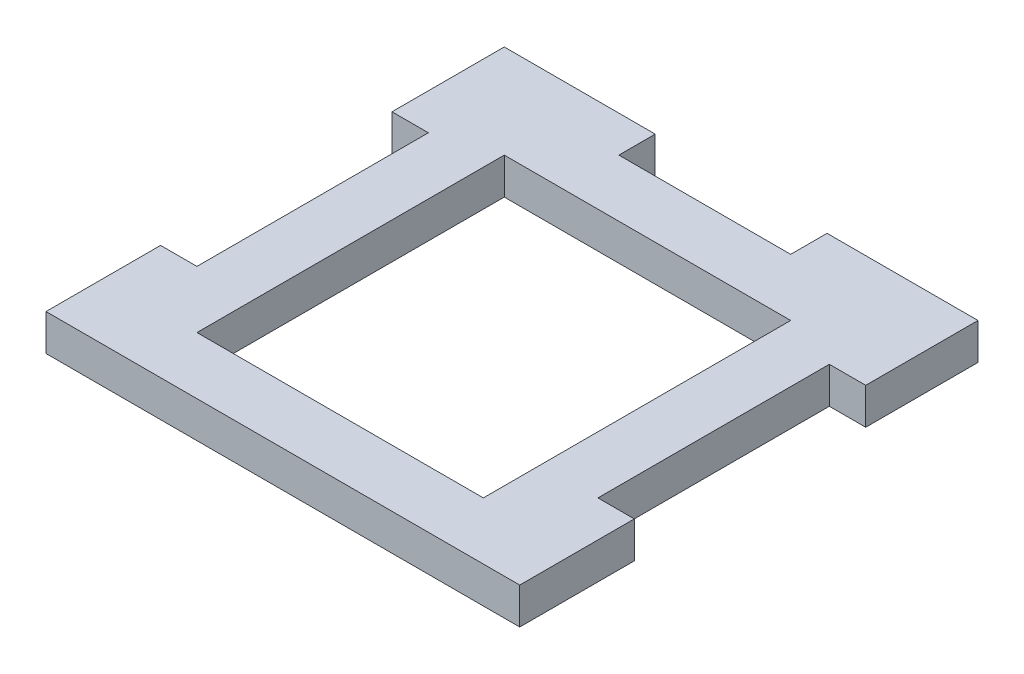
SolidWorks part; units mm, degrees
ref_plane "Front Plane" through (0, 0, 0) normal (0, 0, 1) x (1, 0, 0)
ref_plane "Top Plane" through (0, 0, 0) normal (0, 1, 0) x (1, 0, 0)
ref_plane "Right Plane" through (0, 0, 0) normal (1, 0, 0) x (0, 0, -1)
sketch "Sketch1" plane through (0, 0, 0) normal (0, 1, 0) x (1, 0, 0)
  line L1 (0, 0) -> (41.35, 0)
  line L2 (0, 0) -> (0, 40)
  line L3 (0, 40) -> (41.35, 40)
  line L4 (41.35, 0) -> (41.35, 40)
  dimension "D1" = 41.35
  dimension "D2" = 40
extrude "Boss-Extrude1" add sketch "Sketch1" along normal blind 3.175
sketch "Sketch2" plane through (0, 0, 0) normal (0, -1, 0) x (1, 0, 0)
  line L0 (41.35, 0) -> (41.35, -40) construction
  line L1 (38.175, -30.2) -> (41.35, -30.2)
  line L2 (38.175, -30.2) -> (38.175, -10)
  line L3 (38.175, -10) -> (41.35, -10)
  line L4 (41.35, -30.2) -> (41.35, -10)
  line L5 (41.35, -10) -> (38.175, -10) construction
  line L6 (0, -40) -> (0, 0) construction
  line L7 (3.175, -30.2) -> (0, -30.2)
  line L8 (3.175, -30.2) -> (3.175, -10)
  line L9 (3.175, -10) -> (0, -10)
  line L10 (0, -30.2) -> (0, -10)
  line L11 (3.175, -10) -> (0, -10) construction
  line L12 (41.35, -40) -> (0, -40) construction
  line L13 (13.175, -40) -> (28.175, -40)
  line L14 (13.175, -40) -> (13.175, -36.825)
  line L15 (13.175, -36.825) -> (28.175, -36.825)
  line L16 (28.175, -40) -> (28.175, -36.825)
  point P24 (20.675, -40)
  point P25 (20.675, -36.825)
  dimension "D1" = 3.175
  dimension "D2" = 15
extrude "Cut-Extrude1" cut sketch "Sketch2" against normal through all
sketch "Sketch3" plane through (0, 3.175, 0) normal (0, 1, 0) x (1, 0, 0)
  line L32 (8.175, 31.825) -> (8.175, 5)
  line L33 (8.175, 5) -> (33.175, 5)
  line L34 (33.175, 5) -> (33.175, 31.825)
  line L35 (33.175, 31.825) -> (8.175, 31.825)
  line L36 (8.175, 31.825) -> (8.175, 5)
  line L37 (8.175, 5) -> (33.175, 5)
  line L38 (33.175, 5) -> (33.175, 31.825)
  line L39 (33.175, 31.825) -> (8.175, 31.825)
  dimension "D1" = 5
extrude "Cut-Extrude2" cut sketch "Sketch3" against normal through all
